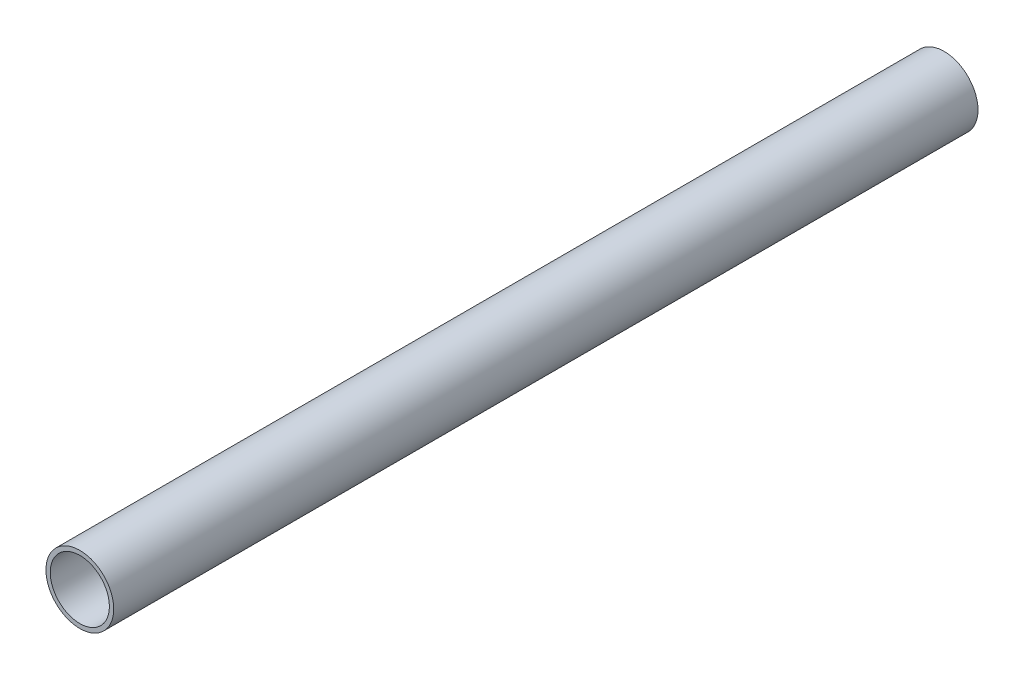
SolidWorks part; units mm, degrees
material "PVC Rigid"
ref_plane "Front Plane" through (0, 0, 0) normal (0, 0, 1) x (1, 0, 0)
ref_plane "Top Plane" through (0, 0, 0) normal (0, 1, 0) x (1, 0, 0)
ref_plane "Right Plane" through (0, 0, 0) normal (1, 0, 0) x (0, 0, -1)
sketch "Sketch1" plane through (0, 0, 0) normal (0, 0, 1) x (1, 0, 0)
  circle A0 centre (0, 0) radius 18.923
  circle A1 centre (0, 0) radius 16.51
  dimension "D1" = 37.846
  dimension "D2" = 33.02
extrude "Boss-Extrude1" add sketch "Sketch1" along normal blind 482.6
